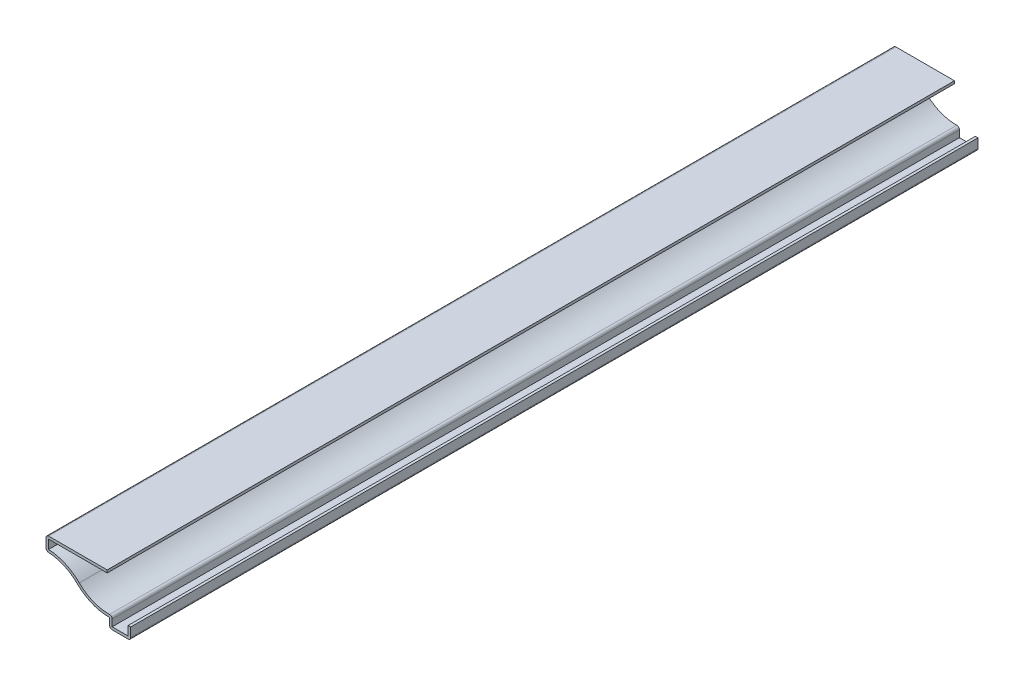
SolidWorks part; units mm, degrees
ref_plane "Front Plane" through (0, 0, 0) normal (0, 0, 1) x (1, 0, 0)
ref_plane "Top Plane" through (0, 0, 0) normal (0, 1, 0) x (1, 0, 0)
ref_plane "Right Plane" through (0, 0, 0) normal (1, 0, 0) x (0, 0, -1)
sketch "Sketch1" plane through (0, 0, 0) normal (0, 0, 1) x (1, 0, 0)
  line L0 (0, 0) -> (0, 16.6687) construction
  line L1 (0, 16.6687) -> (-28.575, 16.6687) construction
  line L2 (0, 3.9688) -> (0, 0)
  line L3 (0, 0) -> (-7.1437, 0)
  line L4 (-7.1437, 0) -> (-7.1438, 3.175)
  line L5 (-28.575, 16.6687) -> (-28.575, 11.9062)
  line L6 (-28.575, 16.6687) -> (-7.9375, 16.6688)
  line L7 (-28.575, 11.9062) -> (-28.575, -3.175) construction
  arc A0 (-7.1438, 3.175) -> (-17.9621, 7.5399) centre (-7.3491, 18.2549) cw
  arc A1 (-17.9621, 7.5399) -> (-28.575, 11.9062) centre (-28.575, -3.175) ccw
  point P10 (0, 0)
  dimension "D7" = 15.0812
  dimension "D1" = 20.6375
  dimension "D2" = 16.6687
  dimension "D3" = 28.575
  dimension "D4" = 4.7625
  dimension "D5" = 3.175
  dimension "D6" = 7.1437
  dimension "D8" = 3.9688
extrude "Extrude-Thin1" add sketch "Sketch1" against normal blind 285.75 thin
fillet "Fillet1" radius 0.889 5 edges at (0, 0, -142.875) (-7.1437, 0, -142.875) (-6.2548, 4.1049, -142.875) (-28.575, 11.9062, -142.875) (-28.575, 16.6687, -142.875)
